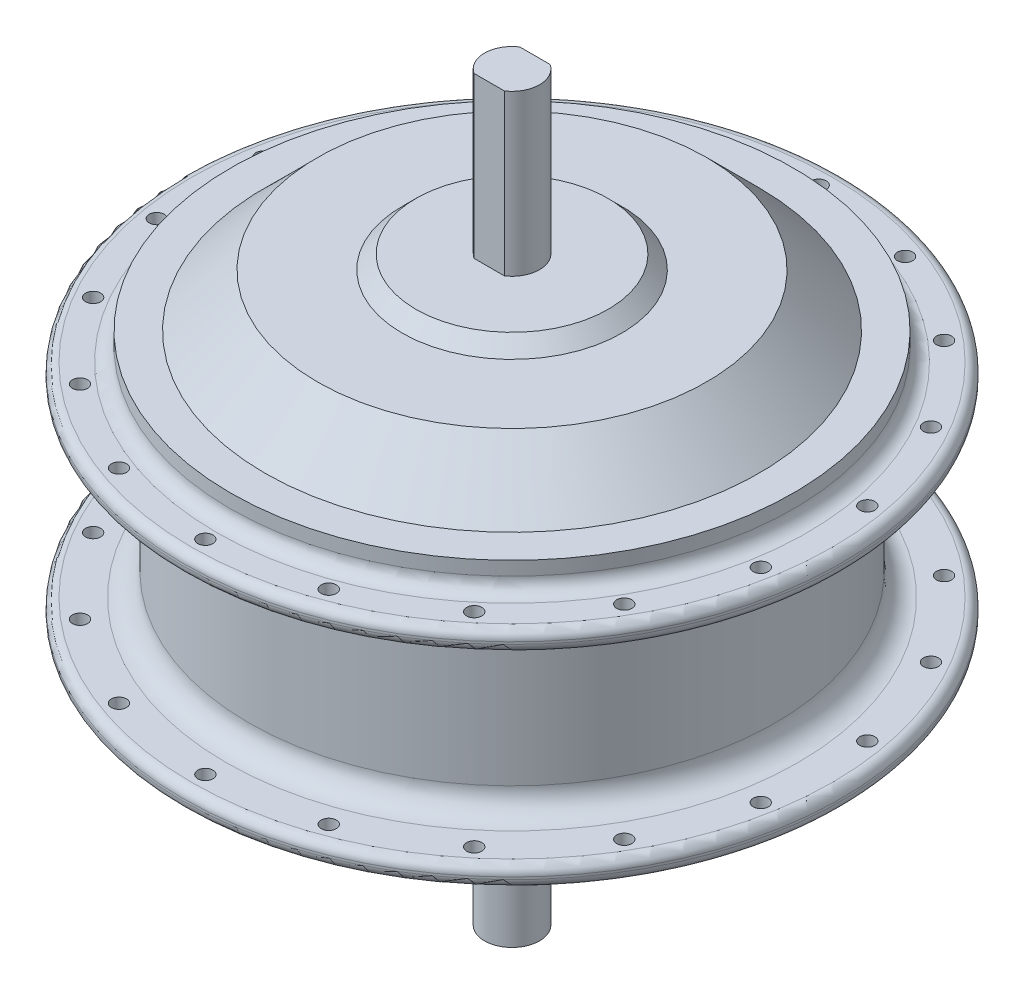
SolidWorks part; units mm, degrees
ref_plane "Спереди" through (0, 0, 0) normal (0, 0, 1) x (1, 0, 0)
ref_plane "Сверху" through (0, 0, 0) normal (0, 1, 0) x (1, 0, 0)
ref_plane "Справа" through (0, 0, 0) normal (1, 0, 0) x (0, 0, -1)
sketch "Эскиз1" plane through (0, 0, 0) normal (1, 0, 0) x (0, 0, -1)
  line L0 (0, -498.2504) -> (0, 24414.2701) construction
  line L1 (0, 80) -> (-6, 80)
  line L2 (-6, 80) -> (-6, 45)
  line L3 (-6, 45) -> (-21, 45)
  line L4 (-21, 45) -> (-24, 42)
  line L5 (-24, 42) -> (-42.5, 42)
  line L6 (-42.5, 42) -> (-54, 30.5)
  line L7 (-54, 30.5) -> (-61.5, 30.5)
  line L8 (-61.5, 30.5) -> (-61.5, 24.5)
  line L9 (-61.5, 24.5) -> (-72, 24.5)
  line L10 (-72, 24.5) -> (-72, 20)
  line L11 (-72, 20) -> (-57.5, 20)
  line L12 (-57.5, 20) -> (-57.5, -20)
  line L13 (-57.5, -20) -> (-72, -20)
  line L14 (-72, -20) -> (-72, -24.5)
  line L15 (-72, -24.5) -> (-62, -24.5)
  line L16 (-62, -24.5) -> (-62, -30.5)
  line L17 (-62, -30.5) -> (-54, -30.5)
  line L18 (-54, -30.5) -> (-42.5, -42)
  line L19 (-42.5, -42) -> (-26.65, -42)
  line L20 (-26.65, -42) -> (-26.65, -51)
  line L21 (-26.65, -51) -> (-6, -51)
  line L22 (-6, -51) -> (-6, -82)
  line L23 (-6, -82) -> (0, -82)
  line L24 (-57.5, 0) -> (0, 0) construction
  line L25 (0, 80) -> (0, -82)
  dimension "D1" = 12
  dimension "D2" = 144
  dimension "D3" = 115
  dimension "D4" = 53.3
  dimension "D5" = 123
  dimension "D6" = 124
  dimension "D7" = 108
  dimension "D8" = 108
  dimension "D9" = 85
  dimension "D10" = 85
  dimension "D11" = 48
  dimension "D12" = 42
  dimension "D13" = 35
  dimension "D14" = 3
  dimension "D15" = 4.5
  dimension "D16" = 40
  dimension "D17" = 31
  dimension "D18" = 9
  dimension "D19" = 6
  dimension "D20" = 6
revolve "Повернуть1" add sketch "Эскиз1" angle 360 about L25
fillet "Скругление1" radius 2 4 edges at (0, -24.5, 72) (0, -20, 72) (0, 20, 72) (0, 24.5, 72)
fillet "Скругление2" radius 5 2 edges at (0, 20, 57.5) (0, -20, 57.5)
fillet "Скругление3" radius 3 2 edges at (0, -24.5, 62) (0, 24.5, 61.5)
sketch "Эскиз2" plane through (0, 80, 0) normal (0, 1, 0) x (1, 0, 0)
  line L1 (-3.3166, 5) -> (3.3166, 5)
  line L3 (-3.3166, -5) -> (3.3166, -5)
  circle A0 centre (0, 0) radius 6 construction
  arc A1 (-3.3166, -5) -> (3.3166, -5) centre (0, 0) ccw
  arc A2 (3.3166, 5) -> (-3.3166, 5) centre (0, 0) ccw
  dimension "D1" = 10
extrude "Вырез-Вытянуть1" cut sketch "Эскиз2" against normal up to surface (35 mm away) up to face at (0, 45, 21)
sketch "Эскиз3" plane through (0, -24.5, 0) normal (0, -1, 0) x (1, 0, 0)
  circle A0 centre (0, 0) radius 67 construction
  circle A1 centre (0, 0) radius 72 construction
  circle A2 centre (0, 67) radius 1.65
  circle A3 centre (22.9153, 62.9594) radius 1.65
  circle A4 centre (43.0668, 51.325) radius 1.65
  circle A5 centre (58.0237, 33.5) radius 1.65
  circle A6 centre (65.9821, 11.6344) radius 1.65
  circle A7 centre (65.9821, -11.6344) radius 1.65
  circle A8 centre (58.0237, -33.5) radius 1.65
  circle A9 centre (43.0668, -51.325) radius 1.65
  circle A10 centre (22.9153, -62.9594) radius 1.65
  circle A11 centre (0, -67) radius 1.65
  circle A12 centre (-22.9153, -62.9594) radius 1.65
  circle A13 centre (-43.0668, -51.325) radius 1.65
  circle A14 centre (-58.0237, -33.5) radius 1.65
  circle A15 centre (-65.9821, -11.6344) radius 1.65
  circle A16 centre (-65.9821, 11.6344) radius 1.65
  circle A17 centre (-58.0237, 33.5) radius 1.65
  circle A18 centre (-43.0668, 51.325) radius 1.65
  circle A19 centre (-22.9153, 62.9594) radius 1.65
  point P44 (0, 0)
  dimension "D1" = 5
  dimension "D2" = 3.3
  dimension "D3" = 18
extrude "Вырез-Вытянуть2" cut sketch "Эскиз3" against normal through all and the other way through all
